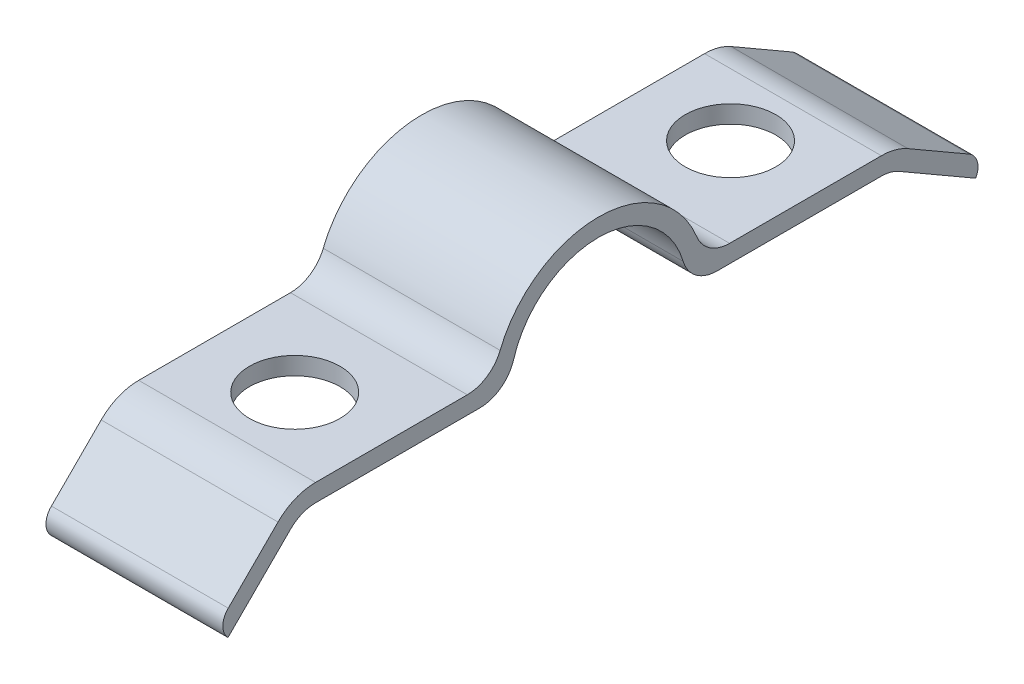
SolidWorks part; units mm, degrees
material "Brass"
ref_plane "Front Plane" through (0, 0, 0) normal (0, 0, 1) x (1, 0, 0)
ref_plane "Top Plane" through (0, 0, 0) normal (0, 1, 0) x (1, 0, 0)
ref_plane "Right Plane" through (0, 0, 0) normal (1, 0, 0) x (0, 0, -1)
sketch "Sketch1" plane through (0, 0, 0) normal (1, 0, 0) x (0, 0, -1)
  line L0 (-10.16, 0) -> (-4.2597, 0)
  line L1 (4.2597, 0) -> (10.16, 0)
  line L2 (-11.058, -0.372) -> (-12.8541, -2.168)
  line L3 (10.795, -0.1701) -> (12.9947, -1.4401)
  line L4 (-10.16, 0.635) -> (-4.7093, 0.635)
  line L5 (-11.507, 0.077) -> (-13.2929, -1.7089)
  line L6 (-12.8541, -2.168) -> (-13.3032, -2.6172)
  line L7 (10.16, 0.635) -> (4.7093, 0.635)
  line L8 (11.1125, 0.3798) -> (13.3122, -0.8902)
  line L9 (12.9947, -1.4401) -> (13.5446, -1.7576)
  arc A0 (3.0426, 0.9071) -> (-3.0426, 0.9071) centre (0, 0) ccw
  arc A1 (-10.16, 0) -> (-11.058, -0.372) centre (-10.16, -1.27) ccw
  arc A2 (3.532, 1.4288) -> (-3.532, 1.4287) centre (0, 0) ccw
  arc A3 (10.795, -0.1701) -> (10.16, 0) centre (10.16, -1.27) ccw
  arc A4 (-10.16, 0.635) -> (-11.507, 0.077) centre (-10.16, -1.27) ccw
  arc A5 (11.1125, 0.3798) -> (10.16, 0.635) centre (10.16, -1.27) ccw
  arc A6 (-13.2929, -1.7089) -> (-13.3032, -2.6172) centre (-12.8541, -2.168) ccw
  arc A7 (13.5446, -1.7576) -> (13.3122, -0.8902) centre (12.9947, -1.4401) ccw
  arc A8 (4.2597, 0) -> (3.0426, 0.9071) centre (4.2597, 1.27) cw
  arc A9 (-4.2597, 0) -> (-3.0426, 0.9071) centre (-4.2597, 1.27) ccw
  arc A10 (-4.7093, 0.635) -> (-3.532, 1.4287) centre (-4.7093, 1.905) ccw
  arc A11 (4.7093, 0.635) -> (3.532, 1.4288) centre (4.7093, 1.905) cw
  point P9 (3.175, 0)
  point P17 (-3.175, 0)
  dimension "D1" = 6.35
  dimension "D4" = 2.54
  dimension "D6" = 7.62
  dimension "D7" = 2.54
  dimension "D11" = 3.81
  dimension "D12" = 3.81
  dimension "D13" = 1.2703
  dimension "D14" = 1.27
  dimension "D2" = 10.16
  dimension "D3" = 10.16
  dimension "D5" = 135
  dimension "D8" = 150
  dimension "D9" = 2.54
  dimension "D10" = 2.54
extrude "Boss-Extrude1" add sketch "Sketch1" along normal mid plane 6.35
sketch "Sketch2" plane through (0, 0.635, 0) normal (0, 1, 0) x (1, 0, 0)
  circle A0 centre (0, -7.7318) radius 1.6256
  circle A1 centre (0, 7.9172) radius 1.6256
  dimension "D3" = 3.2512
  dimension "D1" = 7.7318
  dimension "D2" = 7.9172
extrude "Cut-Extrude1" cut sketch "Sketch2" against normal up to next and the other way through all
equation "\"D3@Sketch1\"=\"D2@Sketch1\""
equation "\"D7@Sketch1\"=\"D4@Sketch1\""
equation "\"D2@Sketch2\"=0.3117"
